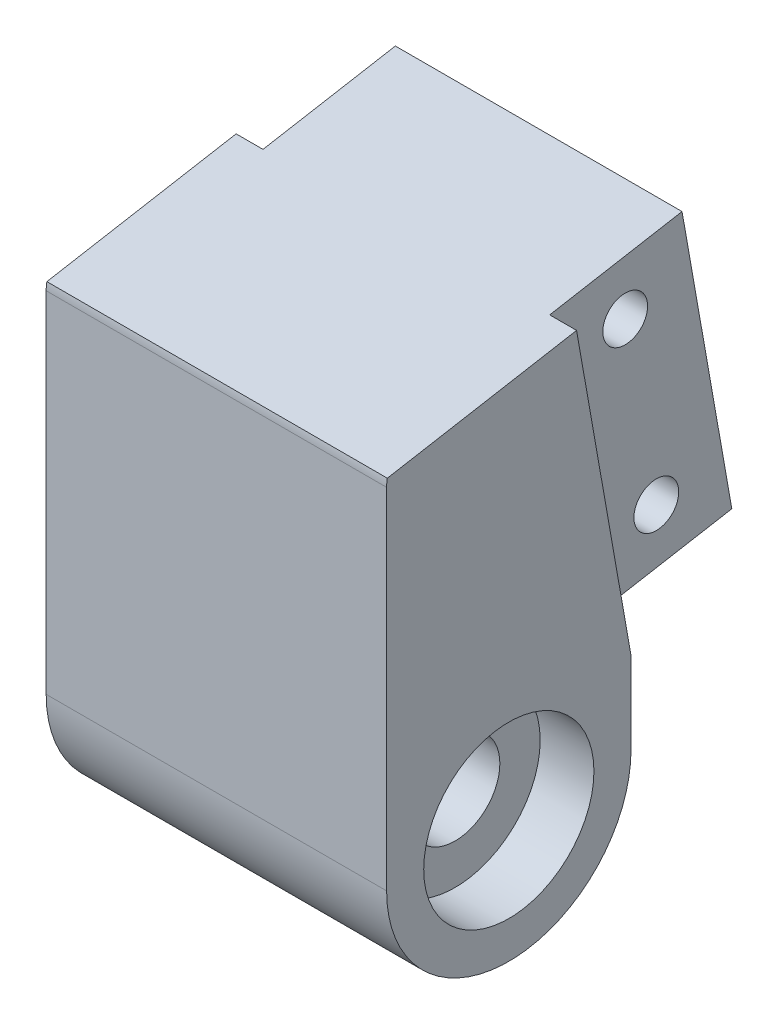
SolidWorks part; units mm, degrees
material "6061-T6 (SS)"
ref_plane "Front Plane" through (0, 0, 0) normal (0, 0, 1) x (1, 0, 0)
ref_plane "Top Plane" through (0, 0, 0) normal (0, 1, 0) x (1, 0, 0)
ref_plane "Right Plane" through (0, 0, 0) normal (1, 0, 0) x (0, 0, -1)
sketch "Sketch1" plane through (0, 0, 0) normal (1, 0, 0) x (0, 0, -1)
  line L0 (18.0278, -4.1409) -> (49.6634, 1.4374)
  line L1 (49.6634, 1.4374) -> (56.2621, -35.9853)
  line L2 (56.2621, -35.9853) -> (41.4899, -38.5901)
  line L3 (41.4899, -38.5901) -> (41.4899, -47.702)
  line L5 (14.2104, -47.702) -> (14.2104, -8.6903)
  line L6 (14.2104, -4.814) -> (14.2104, 93.9179) construction
  line L7 (52.9627, -17.274) -> (27.8502, -21.702) construction
  circle A0 centre (27.8502, -47.702) radius 5
  arc A1 (18.0278, -4.1409) -> (14.2104, -8.6903) centre (18.83, -8.6903) ccw
  arc A2 (14.2104, -47.702) -> (41.4899, -47.702) centre (27.8502, -47.702) ccw
  dimension "D6" = 10
  dimension "D8" = 4.6196
  dimension "D1" = 80
  dimension "D2" = 38
  dimension "D3" = 36
  dimension "D4" = 15
  dimension "D7" = 26
extrude "Boss-Extrude1" add sketch "Sketch1" along normal blind 38
sketch "Sketch2" plane through (38, 0, 0) normal (1, 0, 0) x (0, 0, -1)
  circle A0 centre (27.8502, -47.702) radius 9.5
  dimension "D1" = 19
extrude "Cut-Extrude1" cut sketch "Sketch2" against normal blind 6
ref_plane "Plane1" through (19, 0, 0) normal (1, 0, 0) x (0, 0, -1)
mirror "Mirror1" about plane through (19, 0, 0) normal (1, 0, 0) of "Cut-Extrude1"
sketch "Sketch3" plane through (0, 8.5363, -48.4117) normal (0, 0.1736, -0.9848) x (-1, 0, 0)
  line L0 (-19, 15.8682) -> (-19, -15.8682) construction
  line L1 (-38, -45.2084) -> (0, -45.2084)
  line L2 (-38, -45.2084) -> (-38, -7.2084)
  line L3 (-38, -7.2084) -> (0, -7.2084)
  line L4 (0, -45.2084) -> (0, -7.2084)
  line L5 (-38, -45.2084) -> (0, -7.2084) construction
  line L6 (-38, -7.2084) -> (0, -45.2084) construction
  line L8 (-35, -10.2084) -> (-3, -10.2084)
  line L9 (-35, -10.2084) -> (-35, -42.2084)
  line L10 (-35, -42.2084) -> (-3, -42.2084)
  line L11 (-3, -10.2084) -> (-3, -42.2084)
  line L12 (-35, -10.2084) -> (-3, -42.2084) construction
  line L13 (-35, -42.2084) -> (-3, -10.2084) construction
  point P0 (-19, -26.2084)
  point P11 (-19, -26.2084)
  dimension "D1" = 32
extrude "Cut-Extrude2" cut sketch "Sketch3" against normal up to vertex (15 mm away)
sketch "Sketch4" plane through (0, 5.9316, -33.6396) normal (0, 0.1736, -0.9848) x (-1, 0, 0)
  line L0 (0, -45.2084) -> (0, -7.2084) construction
  line L1 (-38, -7.2084) -> (0, -7.2084)
  line L2 (-38, -7.2084) -> (-38, -10.2084)
  line L3 (-38, -10.2084) -> (0, -10.2084)
  line L4 (0, -7.2084) -> (0, -10.2084)
  dimension "D1" = 3
extrude "Cut-Extrude3" cut sketch "Sketch4" against normal through all
sketch "Sketch6" plane through (35, 0, 0) normal (1, 0, 0) x (0, 0, -1)
  line L0 (42.7983, -2.8194) -> (48.3551, -34.3333) construction
  line L1 (35.4123, -4.1218) -> (50.1844, -1.5171) construction
  line L2 (40.969, -35.6356) -> (55.7411, -33.0309) construction
  circle A0 centre (43.8402, -8.7283) radius 2.5
  circle A1 centre (47.3132, -28.4244) radius 2.5
  dimension "D1" = 5
  dimension "D2" = 5
  dimension "D3" = 6
  dimension "D4" = 6
extrude "Cut-Extrude4" cut sketch "Sketch6" against normal through all
